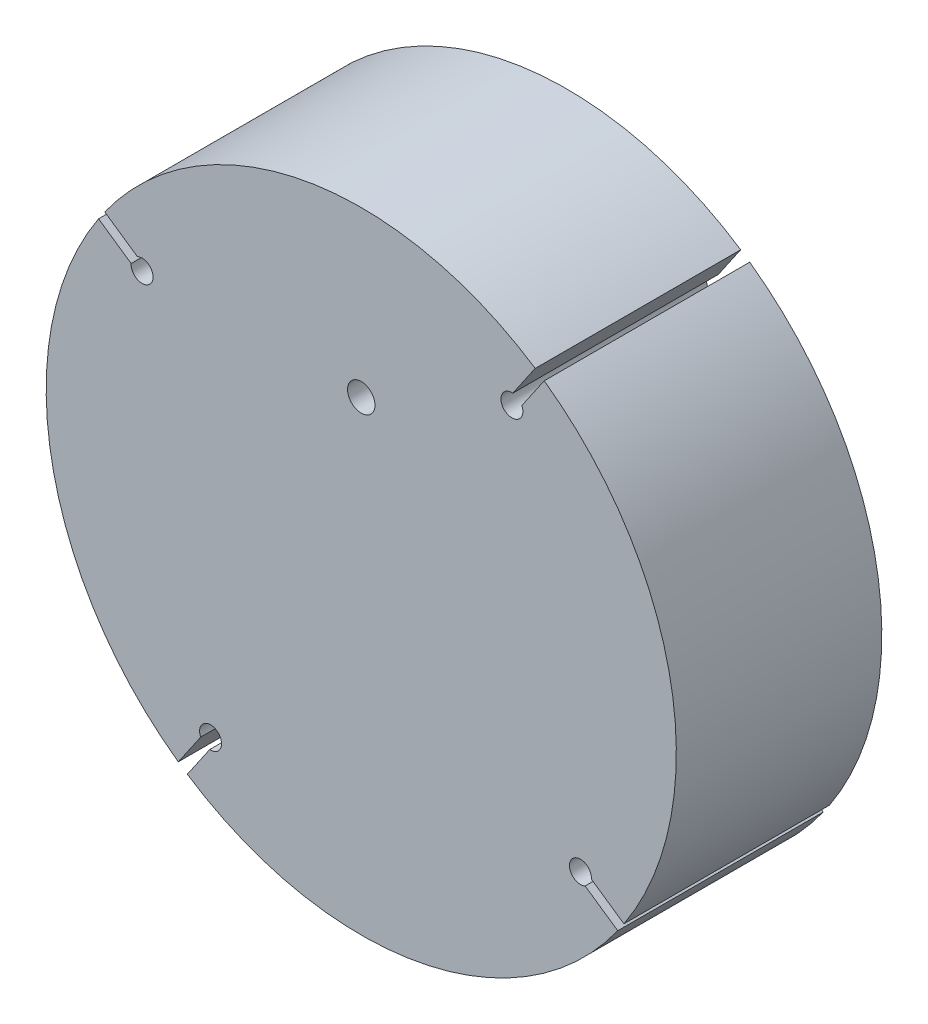
SolidWorks part; units mm, degrees
ref_plane "Piano frontale" through (0, 0, 0) normal (0, 0, 1) x (1, 0, 0)
ref_plane "Piano superiore" through (0, 0, 0) normal (0, 1, 0) x (1, 0, 0)
ref_plane "Piano destro" through (0, 0, 0) normal (1, 0, 0) x (0, 0, -1)
sketch "Schizzo1" plane through (0, 0, 0) normal (0, 0, 1) x (1, 0, 0)
  line L0 (0, 0) -> (0, 59.0251) construction
  line L1 (0, 0) -> (74.1691, 0) construction
  line L2 (0, 0) -> (-72.162, 0) construction
  line L3 (0, 0) -> (0, -57.3829) construction
  circle A0 centre (0, 0) radius 115
extrude "Estrusione-Estrusione1" add sketch "Schizzo1" along normal blind 75
sketch "Schizzo2" plane through (0, 0, 0) normal (0, 0, -1) x (-1, 0, 0)
  line L0 (58.6106, -81.7215) -> (66.789, -93.6174)
  line L2 (55.3144, -83.9876) -> (63.4929, -95.8835)
  line L6 (81.7215, 58.6106) -> (93.6174, 66.789)
  line L7 (-58.6106, 81.7215) -> (-66.789, 93.6174)
  line L8 (83.9876, 55.3144) -> (95.8835, 63.4929)
  line L9 (-55.3144, 83.9876) -> (-63.4929, 95.8835)
  line L10 (-81.7215, -58.6106) -> (-93.6174, -66.789)
  line L11 (-83.9876, -55.3144) -> (-95.8835, -63.4929)
  arc A0 (81.7215, 58.6106) -> (83.9876, 55.3144) centre (80, 55) ccw
  arc A1 (-58.6106, 81.7215) -> (-55.3144, 83.9876) centre (-55, 80) ccw
  arc A2 (66.789, -93.6174) -> (63.4929, -95.8835) centre (0, 0) cw
  arc A3 (55.3144, -83.9876) -> (58.6106, -81.7215) centre (55, -80) cw
  arc A4 (-63.4929, 95.8835) -> (-66.789, 93.6174) centre (0, 0) ccw
  arc A6 (95.8835, 63.4929) -> (93.6174, 66.789) centre (0, 0) ccw
  arc A7 (-81.7215, -58.6106) -> (-83.9876, -55.3144) centre (-80, -55) ccw
  arc A8 (-95.8835, -63.4929) -> (-93.6174, -66.789) centre (0, 0) ccw
extrude "Taglio-Estrusione1" cut sketch "Schizzo2" against normal up to next
sketch "Schizzo3" plane through (0, 0, 0) normal (0, 0, -1) x (-1, 0, 0)
  line L0 (0, 0) -> (-182.6235, 0) construction
  line L1 (-182.6235, 0) -> (198.4906, 0) construction
  line L2 (0, 0) -> (0, 124.0375) construction
  line L3 (0, 124.0375) -> (0, -131.3608) construction
  line L6 (-5, 30) -> (-65, 30)
  line L7 (-5, 30) -> (-5, -30)
  line L8 (-5, -30) -> (-65, -30)
  line L9 (-65, 30) -> (-65, -30)
  line L10 (-5, 30) -> (-65, -30) construction
  line L11 (-5, -30) -> (-65, 30) construction
extrude "Taglio-Estrusione2" cut sketch "Schizzo3" against normal blind 15
sketch "Schizzo4" plane through (0, 0, 0) normal (0, 0, -1) x (-1, 0, 0)
  line L0 (0, 0) -> (190.2519, 0) construction
  line L1 (0, 0) -> (0, 121.9016) construction
  line L2 (0, 121.9016) -> (0, -128.9197) construction
  line L5 (15, -35) -> (65, -35)
  line L6 (15, -35) -> (15, 35)
  line L7 (15, 35) -> (65, 35)
  line L8 (65, -35) -> (65, 35)
  line L9 (15, -35) -> (65, 35) construction
  line L10 (15, 35) -> (65, -35) construction
extrude "Taglio-Estrusione3" cut sketch "Schizzo4" against normal blind 25
sketch "Schizzo5" plane through (0, 0, 0) normal (0, 0, -1) x (-1, 0, 0)
  line L0 (0, 0) -> (0, 123.1221) construction
  circle A0 centre (0, 55) radius 5
extrude "Taglio-Estrusione4" cut sketch "Schizzo5" against normal through all
sketch "Schizzo6" plane through (0, 0, 0) normal (0, 0, -1) x (-1, 0, 0)
  line L0 (0, 0) -> (0, 125.8683) construction
  line L3 (-22.5, 107) -> (22.5, 107)
  line L4 (-22.5, 107) -> (-22.5, 62)
  line L5 (-22.5, 62) -> (22.5, 62)
  line L6 (22.5, 107) -> (22.5, 62)
  line L7 (-22.5, 107) -> (22.5, 62) construction
  line L8 (-22.5, 62) -> (22.5, 107) construction
extrude "Taglio-Estrusione5" cut sketch "Schizzo6" against normal blind 12
